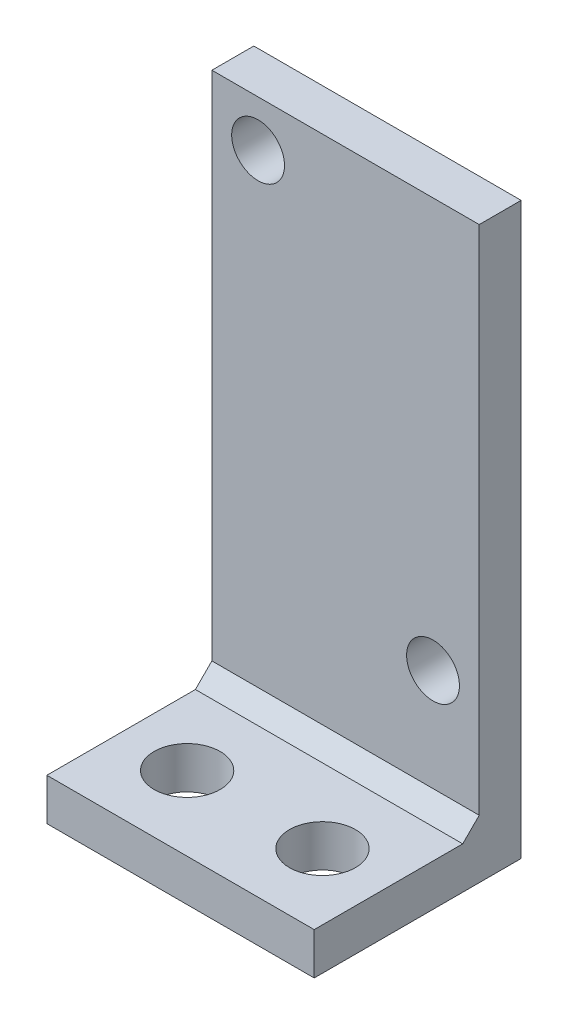
SolidWorks part; units mm, degrees
ref_plane "Front Plane" through (0, 0, 0) normal (0, 0, 1) x (1, 0, 0)
ref_plane "Top Plane" through (0, 0, 0) normal (0, 1, 0) x (1, 0, 0)
ref_plane "Right Plane" through (0, 0, 0) normal (1, 0, 0) x (0, 0, -1)
sketch "Sketch1" plane through (0, 0, 0) normal (0, 0, 1) x (1, 0, 0)
  line L1 (0, 0) -> (16.2, 0)
  line L2 (0, 0) -> (0, 34.54)
  line L3 (0, 34.54) -> (16.2, 34.54)
  line L4 (16.2, 0) -> (16.2, 34.54)
  dimension "D1" = 16.2
  dimension "D2" = 34.54
extrude "Boss-Extrude1" add sketch "Sketch1" along normal blind 2.54
sketch "Sketch2" plane through (0, 0, 2.54) normal (0, 0, 1) x (1, 0, 0)
  line L0 (16.2, 0) -> (16.2, 34.54) construction
  line L1 (0, 0) -> (16.2, 0)
  line L2 (0, 0) -> (0, 2.54)
  line L3 (0, 2.54) -> (16.2, 2.54)
  line L4 (16.2, 0) -> (16.2, 2.54)
  dimension "D1" = 2.54
extrude "Boss-Extrude2" add sketch "Sketch2" along normal blind 10
chamfer "Chamfer1" distance 1 angle 45 1 edges at (8.1, 2.54, 2.54)
sketch "Sketch4" plane through (0, 0, 0) normal (0, 0, -1) x (-1, 0, 0)
  line L1 (-16.2, 34.54) -> (0, 34.54) construction
  line L3 (-8.1, 0) -> (-8.1, 34.54) construction
  line L4 (0, 0) -> (-16.2, 0) construction
  circle A2 centre (-13.4, 9.74) radius 1.6
  circle A3 centre (-2.8, 31.74) radius 1.6
extrude "Cut-Extrude1" cut sketch "Sketch4" against normal blind 2.54
sketch "Sketch5" plane through (0, 2.54, 0) normal (0, 1, 0) x (1, 0, 0)
  line L0 (16.2, -8.04) -> (0, -8.04) construction
  line L1 (16.2, -12.54) -> (16.2, -3.54) construction
  line L2 (0, -12.54) -> (0, -3.54) construction
  circle A0 centre (12.2, -8.04) radius 2
  circle A1 centre (4, -8.04) radius 2
  dimension "D1" = 4
extrude "Cut-Extrude2" cut sketch "Sketch5" against normal through all
